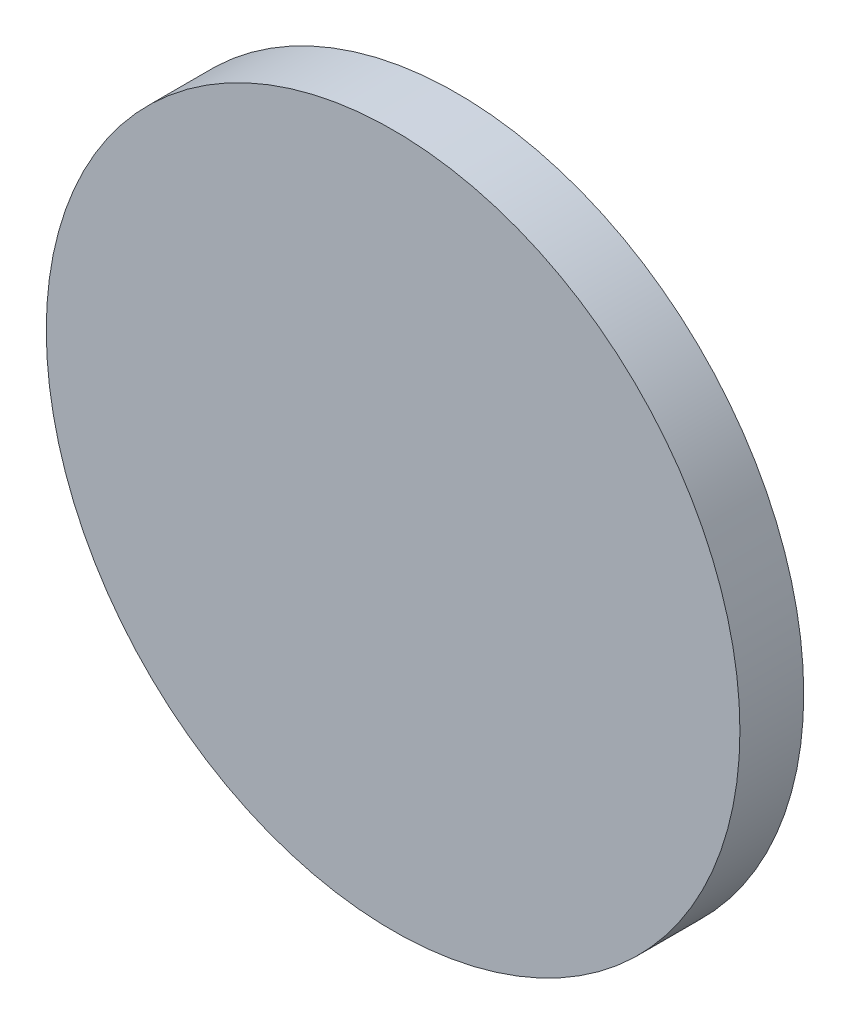
SolidWorks part; units mm, degrees
ref_plane "前视基准面" through (0, 0, 0) normal (0, 0, 1) x (1, 0, 0)
ref_plane "上视基准面" through (0, 0, 0) normal (0, 1, 0) x (1, 0, 0)
ref_plane "右视基准面" through (0, 0, 0) normal (1, 0, 0) x (0, 0, -1)
sketch "草图1" plane through (0, 0, 0) normal (0, 0, 1) x (1, 0, 0)
  circle A0 centre (101.2479, 61.5632) radius 12.5
  dimension "D1" = 25
extrude "凸台-拉伸1" add sketch "草图1" along normal blind 2.3
